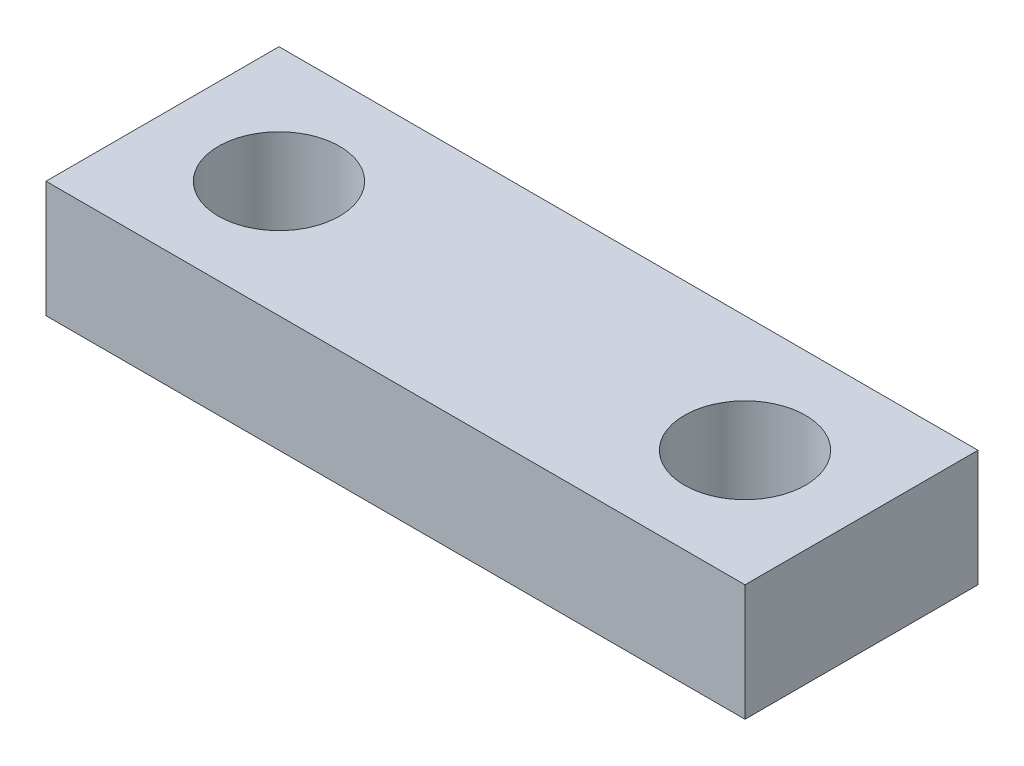
SolidWorks part; units mm, degrees
ref_plane "Front Plane" through (0, 0, 0) normal (0, 0, 1) x (1, 0, 0)
ref_plane "Top Plane" through (0, 0, 0) normal (0, 1, 0) x (1, 0, 0)
ref_plane "Right Plane" through (0, 0, 0) normal (1, 0, 0) x (0, 0, -1)
sketch "Sketch1" plane through (0, 0, 0) normal (0, 1, 0) x (1, 0, 0)
  line L0 (0, 6.35) -> (38.1, 6.35) construction
  line L1 (0, 0) -> (38.1, 0)
  line L2 (0, 0) -> (0, 12.7)
  line L3 (0, 12.7) -> (38.1, 12.7)
  line L4 (38.1, 0) -> (38.1, 12.7)
  circle A0 centre (6.35, 6.35) radius 3.302
  circle A1 centre (31.75, 6.35) radius 3.302
  point P11 (19.05, 6.35)
  dimension "D4" = 6.604
  dimension "D5" = 6.604
  dimension "D1" = 38.1
  dimension "D2" = 12.7
  dimension "D3" = 25.4
  dimension "D6" = 12.7
extrude "Boss-Extrude1" add sketch "Sketch1" along normal blind 6.35
